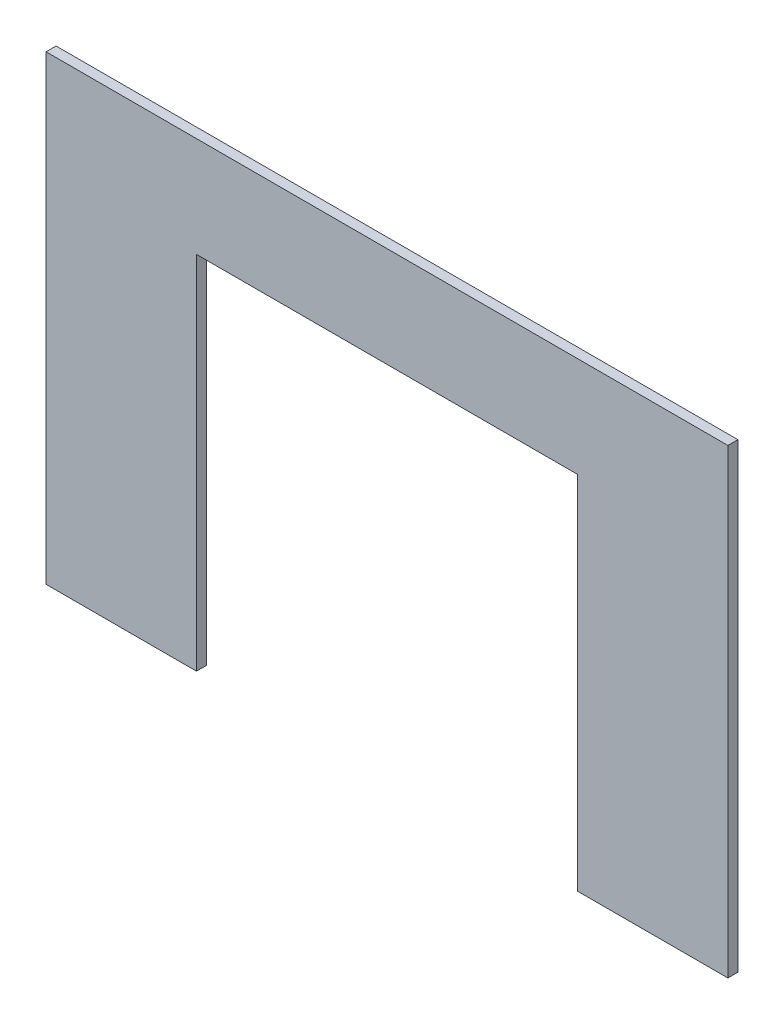
SolidWorks part; units mm, degrees
ref_plane "Front Plane" through (0, 0, 0) normal (0, 0, 1) x (1, 0, 0)
ref_plane "Top Plane" through (0, 0, 0) normal (0, 1, 0) x (1, 0, 0)
ref_plane "Right Plane" through (0, 0, 0) normal (1, 0, 0) x (0, 0, -1)
sketch "Sketch1" plane through (0, 0, 0) normal (0, 0, 1) x (1, 0, 0)
  line L0 (0, 12.7) -> (0, 304.8)
  line L1 (0, 0) -> (431.8, 0) construction
  line L2 (0, 0) -> (0, 304.8) construction
  line L3 (0, 304.8) -> (431.8, 304.8) construction
  line L4 (431.8, 0) -> (431.8, 304.8) construction
  line L5 (0, 304.8) -> (431.8, 304.8)
  line L6 (431.8, 304.8) -> (431.8, 12.7)
  line L7 (431.8, 12.7) -> (336.55, 12.7)
  line L8 (336.55, 12.7) -> (336.55, 241.3)
  line L9 (336.55, 241.3) -> (95.25, 241.3)
  line L10 (95.25, 241.3) -> (95.25, 12.7)
  line L11 (95.25, 12.7) -> (0, 12.7)
  dimension "D1" = 431.8
  dimension "D2" = 304.8
  dimension "D3" = 12.7
  dimension "D4" = 95.25
  dimension "D5" = 241.3
extrude "Boss-Extrude1" add sketch "Sketch1" along normal blind 6.35
